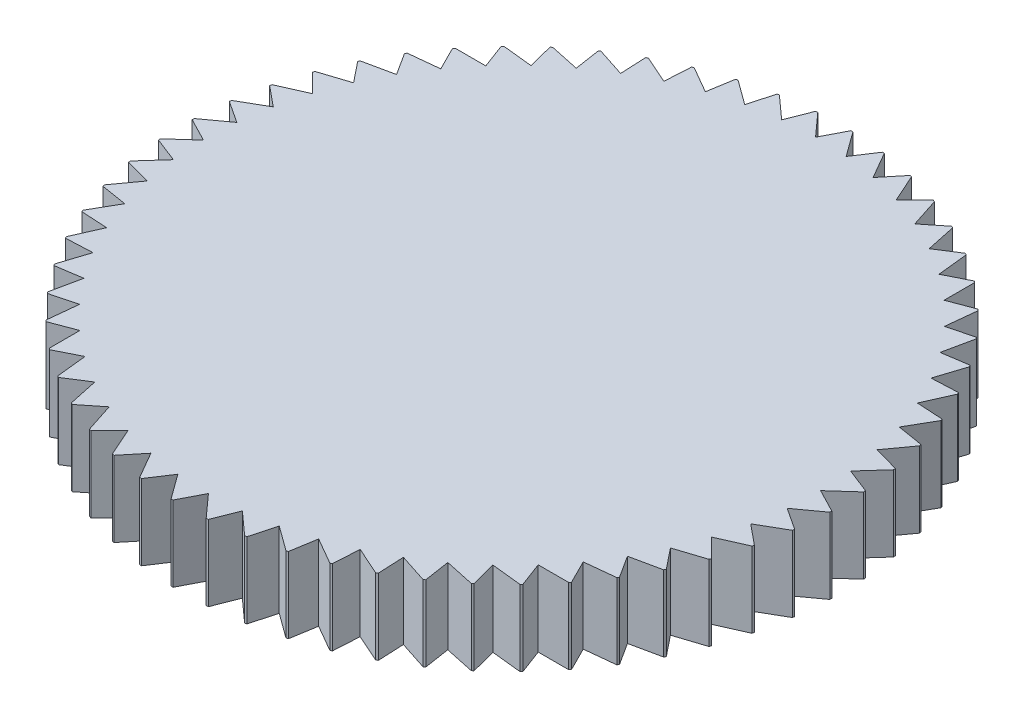
SolidWorks part; units mm, degrees
ref_plane "Ön Düzlem" through (0, 0, 0) normal (0, 0, 1) x (1, 0, 0)
ref_plane "Üst Düzlem" through (0, 0, 0) normal (0, 1, 0) x (1, 0, 0)
ref_plane "Sağ Düzlem" through (0, 0, 0) normal (1, 0, 0) x (0, 0, -1)
sketch "Çizim1" plane through (0, 0, 0) normal (0, 1, 0) x (1, 0, 0)
  line L0 (-9.0308, -9.4621) -> (-8.0544, -9.094)
  line L1 (-8.0544, -9.094) -> (-8.0544, -10.306)
  line L2 (-8.9608, -8.2023) -> (-9.0875, -9.4076)
  line L3 (-9.9704, -8.4663) -> (-8.9608, -8.2023)
  line L4 (-9.7691, -7.2207) -> (-10.0211, -8.4062)
  line L5 (-10.8007, -7.3777) -> (-9.7691, -7.2207)
  line L6 (-10.4704, -6.16) -> (-10.8449, -7.3127)
  line L7 (-11.5128, -6.2083) -> (-10.4704, -6.16)
  line L8 (-11.0569, -5.0318) -> (-11.5499, -6.139)
  line L9 (-12.0986, -4.9709) -> (-11.0569, -5.0318)
  line L10 (-11.5223, -3.8485) -> (-12.1283, -4.8981)
  line L11 (-12.552, -3.679) -> (-11.5223, -3.8485)
  line L12 (-11.8615, -2.623) -> (-12.5738, -3.6035)
  line L13 (-12.8677, -2.3468) -> (-11.8615, -2.623)
  line L14 (-12.0707, -1.3688) -> (-12.8816, -2.2694)
  line L15 (-13.0426, -0.9889) -> (-12.0707, -1.3688)
  line L16 (-12.1476, -0.0995) -> (-13.0483, -0.9105)
  line L17 (-13.0745, 0.3798) -> (-12.1476, -0.0995)
  line L18 (-12.0915, 1.1708) -> (-13.072, 0.4584)
  line L19 (-12.9632, 1.7444) -> (-12.0915, 1.1708)
  line L20 (-11.9028, 2.4283) -> (-12.9524, 1.8223)
  line L21 (-12.7098, 3.0899) -> (-11.9028, 2.4283)
  line L22 (-11.5838, 3.6591) -> (-12.691, 3.1662)
  line L23 (-12.3172, 4.4015) -> (-11.5838, 3.6591)
  line L24 (-11.1379, 4.8499) -> (-12.2905, 4.4754)
  line L25 (-11.7896, 5.6649) -> (-11.1379, 4.8499)
  line L26 (-10.5699, 5.9876) -> (-11.7554, 5.7356)
  line L27 (-11.1329, 6.8662) -> (-10.5699, 5.9876)
  line L28 (-9.8861, 7.0596) -> (-11.0915, 6.933)
  line L29 (-10.3542, 7.9923) -> (-9.8861, 7.0596)
  line L30 (-9.094, 8.0544) -> (-10.306, 8.0544)
  line L31 (-9.4621, 9.0308) -> (-9.094, 8.0544)
  line L32 (-8.2023, 8.9608) -> (-9.4076, 9.0875)
  line L33 (-8.4663, 9.9704) -> (-8.2023, 8.9608)
  line L34 (-7.2207, 9.7691) -> (-8.4062, 10.0211)
  line L35 (-7.3777, 10.8007) -> (-7.2207, 9.7691)
  line L36 (-6.16, 10.4704) -> (-7.3127, 10.8449)
  line L37 (-6.2083, 11.5128) -> (-6.16, 10.4704)
  line L38 (-5.0318, 11.0569) -> (-6.139, 11.5499)
  line L39 (-4.9709, 12.0986) -> (-5.0318, 11.0569)
  line L40 (-3.8485, 11.5223) -> (-4.8981, 12.1283)
  line L41 (-3.679, 12.552) -> (-3.8485, 11.5223)
  line L42 (-2.623, 11.8615) -> (-3.6035, 12.5738)
  line L43 (-2.3468, 12.8677) -> (-2.623, 11.8615)
  line L44 (-1.3688, 12.0707) -> (-2.2694, 12.8816)
  line L45 (-0.9889, 13.0426) -> (-1.3688, 12.0707)
  line L46 (-0.0995, 12.1476) -> (-0.9105, 13.0483)
  line L47 (0.3798, 13.0745) -> (-0.0995, 12.1476)
  line L48 (1.1708, 12.0915) -> (0.4584, 13.072)
  line L49 (1.7444, 12.9632) -> (1.1708, 12.0915)
  line L50 (2.4283, 11.9028) -> (1.8223, 12.9524)
  line L51 (3.0899, 12.7098) -> (2.4283, 11.9028)
  line L52 (3.6591, 11.5838) -> (3.1662, 12.691)
  line L53 (4.4015, 12.3172) -> (3.6591, 11.5838)
  line L54 (4.8499, 11.1379) -> (4.4754, 12.2905)
  line L55 (5.6649, 11.7896) -> (4.8499, 11.1379)
  line L56 (5.9876, 10.5699) -> (5.7356, 11.7554)
  line L57 (6.8662, 11.1329) -> (5.9876, 10.5699)
  line L58 (7.0596, 9.8861) -> (6.933, 11.0915)
  line L59 (7.9923, 10.3542) -> (7.0596, 9.8861)
  line L60 (8.0544, 9.094) -> (8.0544, 10.306)
  line L61 (9.0308, 9.4621) -> (8.0544, 9.094)
  line L62 (8.9608, 8.2023) -> (9.0875, 9.4076)
  line L63 (9.9704, 8.4663) -> (8.9608, 8.2023)
  line L64 (9.7691, 7.2207) -> (10.0211, 8.4062)
  line L65 (10.8007, 7.3777) -> (9.7691, 7.2207)
  line L66 (10.4704, 6.16) -> (10.8449, 7.3127)
  line L67 (11.5128, 6.2083) -> (10.4704, 6.16)
  line L68 (11.0569, 5.0318) -> (11.5499, 6.139)
  line L69 (12.0986, 4.9709) -> (11.0569, 5.0318)
  line L70 (11.5223, 3.8485) -> (12.1283, 4.8981)
  line L71 (12.552, 3.679) -> (11.5223, 3.8485)
  line L72 (11.8615, 2.623) -> (12.5738, 3.6035)
  line L73 (12.8677, 2.3468) -> (11.8615, 2.623)
  line L74 (12.0707, 1.3688) -> (12.8816, 2.2694)
  line L75 (13.0426, 0.9889) -> (12.0707, 1.3688)
  line L76 (12.1476, 0.0995) -> (13.0483, 0.9105)
  line L77 (13.0745, -0.3798) -> (12.1476, 0.0995)
  line L78 (12.0915, -1.1708) -> (13.072, -0.4584)
  line L79 (12.9632, -1.7444) -> (12.0915, -1.1708)
  line L80 (11.9028, -2.4283) -> (12.9524, -1.8223)
  line L81 (12.7098, -3.0899) -> (11.9028, -2.4283)
  line L82 (11.5838, -3.6591) -> (12.691, -3.1662)
  line L83 (12.3172, -4.4015) -> (11.5838, -3.6591)
  line L84 (11.1379, -4.8499) -> (12.2905, -4.4754)
  line L85 (11.7896, -5.6649) -> (11.1379, -4.8499)
  line L86 (10.5699, -5.9876) -> (11.7554, -5.7356)
  line L87 (11.1329, -6.8662) -> (10.5699, -5.9876)
  line L88 (9.8861, -7.0596) -> (11.0915, -6.933)
  line L89 (10.3542, -7.9923) -> (9.8861, -7.0596)
  line L90 (9.094, -8.0544) -> (10.306, -8.0544)
  line L91 (9.4621, -9.0308) -> (9.094, -8.0544)
  line L92 (8.2023, -8.9608) -> (9.4076, -9.0875)
  line L93 (8.4663, -9.9704) -> (8.2023, -8.9608)
  line L94 (7.2207, -9.7691) -> (8.4062, -10.0211)
  line L95 (7.3777, -10.8007) -> (7.2207, -9.7691)
  line L96 (6.16, -10.4704) -> (7.3127, -10.8449)
  line L97 (6.2083, -11.5128) -> (6.16, -10.4704)
  line L98 (5.0318, -11.0569) -> (6.139, -11.5499)
  line L99 (4.9709, -12.0986) -> (5.0318, -11.0569)
  line L100 (3.8485, -11.5223) -> (4.8981, -12.1283)
  line L101 (3.679, -12.552) -> (3.8485, -11.5223)
  line L102 (2.623, -11.8615) -> (3.6035, -12.5738)
  line L103 (2.3468, -12.8677) -> (2.623, -11.8615)
  line L104 (1.3688, -12.0707) -> (2.2694, -12.8816)
  line L105 (0.9889, -13.0426) -> (1.3688, -12.0707)
  line L106 (0.0995, -12.1476) -> (0.9105, -13.0483)
  line L107 (-0.3798, -13.0745) -> (0.0995, -12.1476)
  line L108 (-1.1708, -12.0915) -> (-0.4584, -13.072)
  line L109 (-1.7444, -12.9632) -> (-1.1708, -12.0915)
  line L110 (-2.4283, -11.9028) -> (-1.8223, -12.9524)
  line L111 (-3.0899, -12.7098) -> (-2.4283, -11.9028)
  line L112 (-3.6591, -11.5838) -> (-3.1662, -12.691)
  line L113 (-4.4015, -12.3172) -> (-3.6591, -11.5838)
  line L114 (-4.8499, -11.1379) -> (-4.4754, -12.2905)
  line L115 (-5.6649, -11.7896) -> (-4.8499, -11.1379)
  line L116 (-5.9876, -10.5699) -> (-5.7356, -11.7554)
  line L117 (-6.8662, -11.1329) -> (-5.9876, -10.5699)
  line L118 (-7.0596, -9.8861) -> (-6.933, -11.0915)
  line L119 (-7.9923, -10.3542) -> (-7.0596, -9.8861)
  circle A0 centre (0, 0) radius 13.08
  point P156 (0, 0)
  dimension "D1" = 26.16
  dimension "D2" = 60
extrude "Yükseklik-Ekstrüzyon1" add sketch "Çizim1" along normal blind 3 contours L106 A0 L105 L104 L103 L102 L101 L100 L99 L98 L97 L96 L95 L94 L93 L92 L91 L90 L89 L88 L87 L86 L85 L84 L83 L82 L81 L80 L79 L78 L77 L76 L75 L74 L73
